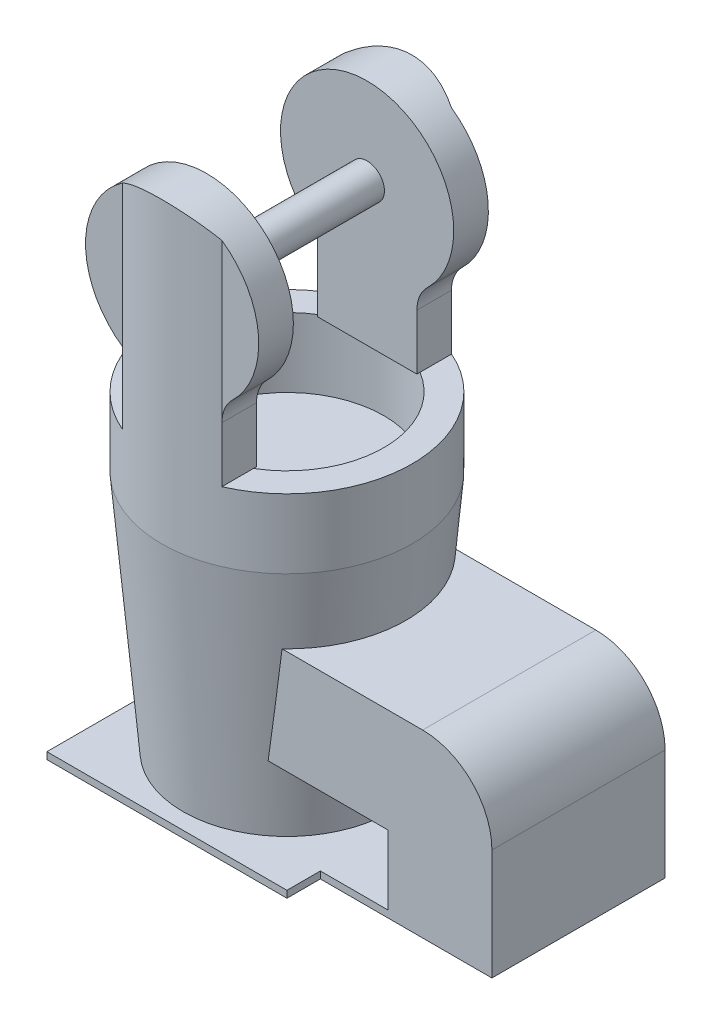
SolidWorks part; units mm, degrees
ref_plane "Front Plane" through (0, 0, 0) normal (0, 0, 1) x (1, 0, 0)
ref_plane "Top Plane" through (0, 0, 0) normal (0, 1, 0) x (1, 0, 0)
ref_plane "Right Plane" through (0, 0, 0) normal (1, 0, 0) x (0, 0, -1)
sketch "Sketch1" plane through (0, 0, 0) normal (0, 1, 0) x (1, 0, 0)
  line L0 (34.6482, -25) -> (84.1642, -25)
  line L1 (34.6482, -34.6482) -> (-34.6482, -34.6482)
  line L2 (34.6482, -34.6482) -> (34.6482, 34.6482)
  line L3 (34.6482, 34.6482) -> (-34.6482, 34.6482)
  line L4 (-34.6482, -34.6482) -> (-34.6482, 34.6482)
  line L5 (34.6482, -34.6482) -> (-34.6482, 34.6482) construction
  line L6 (34.6482, 34.6482) -> (-34.6482, -34.6482) construction
  line L8 (84.1642, -25) -> (84.1642, 25)
  line L9 (34.6482, 25) -> (84.1642, 25)
  line L10 (34.6482, -0.0094) -> (84.1642, 25) construction
  line L11 (84.1642, -25) -> (34.6482, 0.0094) construction
  point P0 (0, 0)
  point P6 (0, 0)
  point P7 (34.6668, 0)
  point P8 (0, 0)
extrude "Boss-Extrude1" add sketch "Sketch1" along normal blind 2 contours L4 L1 L2 L3 | L9 L2 L0 L8
sketch "Sketch2" plane through (0, 2, 0) normal (0, 1, 0) x (1, 0, 0)
  circle A0 centre (0, 0) radius 30
extrude "Boss-Extrude2" add sketch "Sketch2" along normal blind 70 draft 5 draft outward yes
sketch "Sketch3" plane through (0, 72, 0) normal (0, 1, 0) x (1, 0, 0)
  circle A0 centre (0, 0) radius 36.1242
extrude "Boss-Extrude3" add sketch "Sketch3" along normal blind 20
sketch "Sketch4" plane through (0, 92, 0) normal (0, 1, 0) x (1, 0, 0)
  circle A0 centre (0, 0) radius 28
extrude "Cut-Extrude2" cut sketch "Sketch4" against normal blind 20 contours A0
sketch "Sketch5" plane through (0, 2, 0) normal (0, 1, 0) x (1, 0, 0)
  line L0 (84.1642, 25) -> (84.1642, -25)
  line L1 (84.1642, 25) -> (54.1642, 25)
  line L2 (84.1642, -25) -> (54.1642, -25)
  line L3 (54.1642, 25) -> (54.1642, -25)
extrude "Boss-Extrude4" add sketch "Sketch5" along normal blind 50
sketch "Sketch6" plane through (54.1642, 0, 0) normal (-1, 0, 0) x (0, 0, 1)
  line L0 (-25, 52) -> (25, 52)
  line L1 (-25, 52) -> (-25, 22)
  line L2 (25, 52) -> (25, 22)
  line L3 (-25, 22) -> (25, 22)
extrude "Boss-Extrude5" add sketch "Sketch6" along normal blind 40
fillet "Fillet1" radius 20 1 edges at (84.1642, 52, 0)
sketch "Sketch7" plane through (0, 92, 0) normal (0, 1, 0) x (1, 0, 0)
  line L23 (14.3626, -33.1463) -> (-14.3626, -33.1463)
  line L32 (14.3626, 33.1463) -> (-14.3626, 33.1463)
  line L36 (-14.3626, 33.1463) -> (-37.7728, 33.1463)
  line L37 (-14.3626, -33.1463) -> (-37.7728, -33.1463)
  line L38 (-37.7728, 33.1463) -> (-37.7728, -33.1463)
  line L40 (14.3626, 33.1463) -> (38.5702, 33.1463)
  line L41 (14.3626, -33.1463) -> (38.5702, -33.1463)
  line L42 (38.5702, 33.1463) -> (38.5702, -33.1463)
  line L43 (-37.7728, -33.1463) -> (-37.7728, -23.1463)
  line L44 (-37.7728, 33.1463) -> (-37.7728, 23.1463)
  line L45 (-37.7728, 23.1463) -> (38.5702, 23.1463)
  line L46 (-37.7728, -23.1463) -> (38.5702, -23.1463)
  circle A1 centre (0, 0) radius 36.1242 construction
  point P0 (0, 0)
  circle M6 centre (0, 0) radius 28
  circle M7 centre (0, 0) radius 36.1242
extrude "Boss-Extrude11" add sketch "Sketch7" along normal blind 70 contours L45 L42 L40 M7 | L45 L32 M7 M6 | L38 L45 L36 M7 | L32 M7 | L45 M6 | L46 L38 L37 M7 | L46 L23 M7 M6 | L46 L41 L42 M7 | L46 M6 | L23 M7
sketch "Sketch20" plane through (0, 0, 33.1463) normal (0, 0, 1) x (1, 0, 0)
  line L0 (-14.3626, 92) -> (-14.3626, 112.6551)
  line L1 (-14.3626, 162) -> (-14.3626, 92) construction
  line L2 (14.3626, 92) -> (14.3626, 107.9887)
  line L3 (14.3626, 162) -> (14.3626, 92) construction
  line L4 (-14.3626, 92) -> (-37.7728, 92)
  line L5 (-37.7728, 92) -> (-37.7728, 162)
  line L6 (-37.7728, 162) -> (38.5702, 162)
  line L7 (38.5702, 162) -> (38.5702, 92)
  line L8 (38.5702, 92) -> (14.3626, 92)
  arc A0 (17.4018, 115.1684) -> (-14.3626, 112.6551) centre (0, 133.1177) ccw
  arc A1 (14.3626, 107.9887) -> (17.4018, 115.1684) centre (24.3626, 107.9887) cw
  point P21 (14.3626, 112.6551)
  dimension "D1" = 10
extrude "Cut-Extrude22" cut sketch "Sketch20" against normal blind 70 and the other way blind 70
sketch "Sketch22" plane through (0, 0, -23.1463) normal (0, 0, 1) x (1, 0, 0)
  circle A1 centre (0, 133.1177) radius 5
extrude "Boss-Extrude12" add sketch "Sketch22" along normal blind 51 and the other way blind 2
